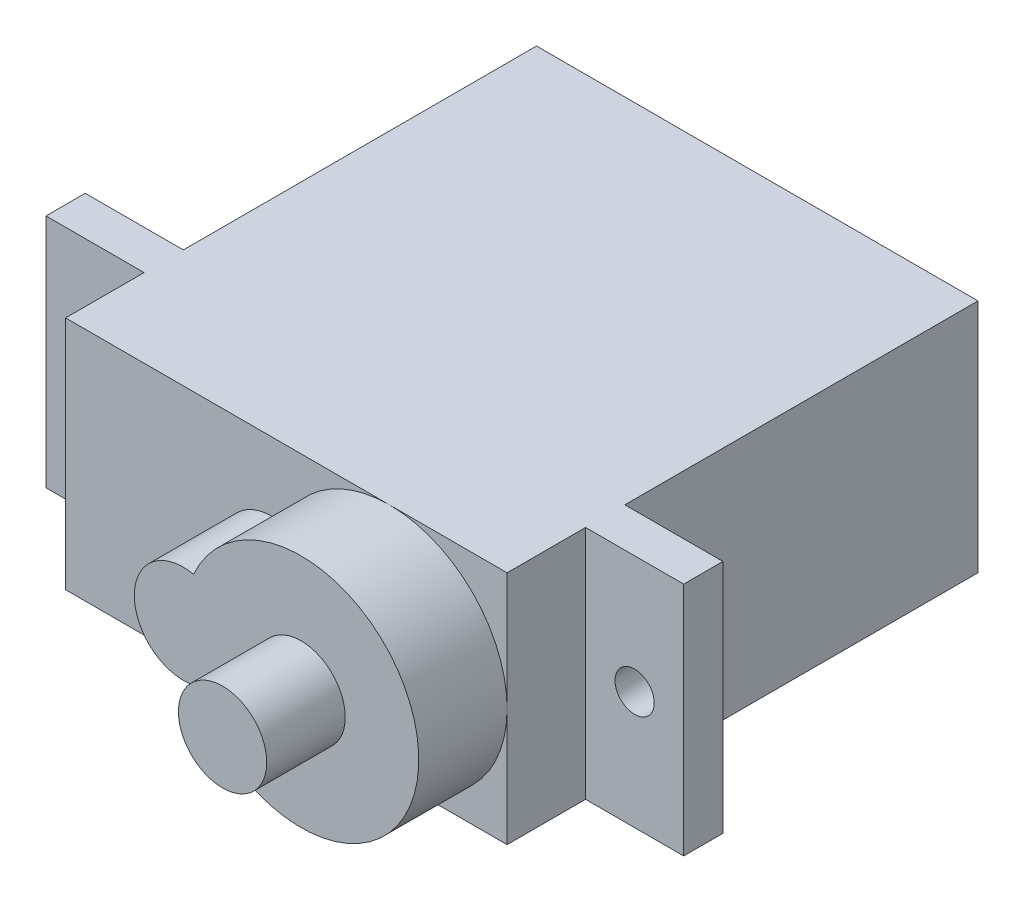
SolidWorks part; units mm, degrees
material "ABS"
ref_plane "前视基准面" through (0, 0, 0) normal (0, 0, 1) x (1, 0, 0)
ref_plane "上视基准面" through (0, 0, 0) normal (0, 1, 0) x (1, 0, 0)
ref_plane "右视基准面" through (0, 0, 0) normal (1, 0, 0) x (0, 0, -1)
sketch "Sketch1" plane through (0, 0, 0) normal (0, 0, 1) x (1, 0, 0)
  line L0 (-11.25, 6) -> (11.25, -6) construction
  line L1 (-11.25, 6) -> (11.25, 6)
  line L2 (-11.25, 6) -> (-11.25, -6)
  line L3 (-11.25, -6) -> (11.25, -6)
  line L4 (11.25, 6) -> (11.25, -6)
  line L5 (-11.25, -6) -> (11.25, 6) construction
  point P5 (0, 0)
  point P6 (0, 0)
  dimension "D1" = 12
  dimension "D2" = 22.5
extrude "Extrude1" add sketch "Sketch1" along normal blind 18
sketch "Sketch2" plane through (0, 0, 18) normal (0, 0, 1) x (1, 0, 0)
  line L1 (-16.25, 6) -> (16.25, 6)
  line L2 (-16.25, 6) -> (-16.25, -6)
  line L3 (-16.25, -6) -> (16.25, -6)
  line L4 (16.25, 6) -> (16.25, -6)
  line L6 (11.25, 6) -> (-11.25, 6) construction
  line L7 (-11.25, -6) -> (11.25, -6) construction
  line L8 (11.25, -6) -> (11.25, 6) construction
  line L9 (-11.25, 6) -> (-11.25, -6) construction
  dimension "D1" = 5
  dimension "D2" = 5
extrude "Extrude2" add sketch "Sketch2" along normal blind 2
sketch "Sketch3" plane through (0, 0, 20) normal (0, 0, 1) x (1, 0, 0)
  line L1 (-11.25, 6) -> (11.25, 6)
  line L2 (-11.25, 6) -> (-11.25, -6)
  line L3 (-11.25, -6) -> (11.25, -6)
  line L4 (11.25, 6) -> (11.25, -6)
extrude "Extrude3" add sketch "Sketch3" along normal blind 4
sketch "Sketch4" plane through (0, 0, 20) normal (0, 0, 1) x (1, 0, 0)
  line L0 (-13.1462, 0) -> (17.5224, 0) construction
  line L1 (11.25, -6) -> (11.25, 6) construction
  line L2 (-11.25, 6) -> (-11.25, -6) construction
  circle A0 centre (-13.75, 0) radius 1
  circle A1 centre (13.75, 0) radius 1
  dimension "D1" = 2
  dimension "D2" = 2
  dimension "D3" = 2.5
  dimension "D4" = 2.5
extrude "Extrude4" cut sketch "Sketch4" against normal through all
sketch "Sketch5" plane through (0, 0, 24) normal (0, 0, 1) x (1, 0, 0)
  line L0 (11.25, -6) -> (11.25, 6) construction
  line L1 (11.25, 6) -> (-11.25, 6) construction
  line L2 (-11.25, -6) -> (11.25, -6) construction
  line L3 (11.25, -6) -> (11.25, 6) construction
  arc A0 (-0.2292, -2.4451) -> (-0.2292, 2.4451) centre (5.25, 0) ccw
  arc A1 (-0.2292, 2.4451) -> (-0.2292, -2.4451) centre (-0.75, 0) ccw
  dimension "D1" = 5
  dimension "D2" = 12
extrude "Extrude5" add sketch "Sketch5" along normal blind 4.5
sketch "Sketch6" plane through (0, 0, 28.5) normal (0, 0, 1) x (1, 0, 0)
  circle A0 centre (5.25, 0) radius 2.25
  dimension "D1" = 4.5
extrude "Extrude6" add sketch "Sketch6" along normal blind 4
